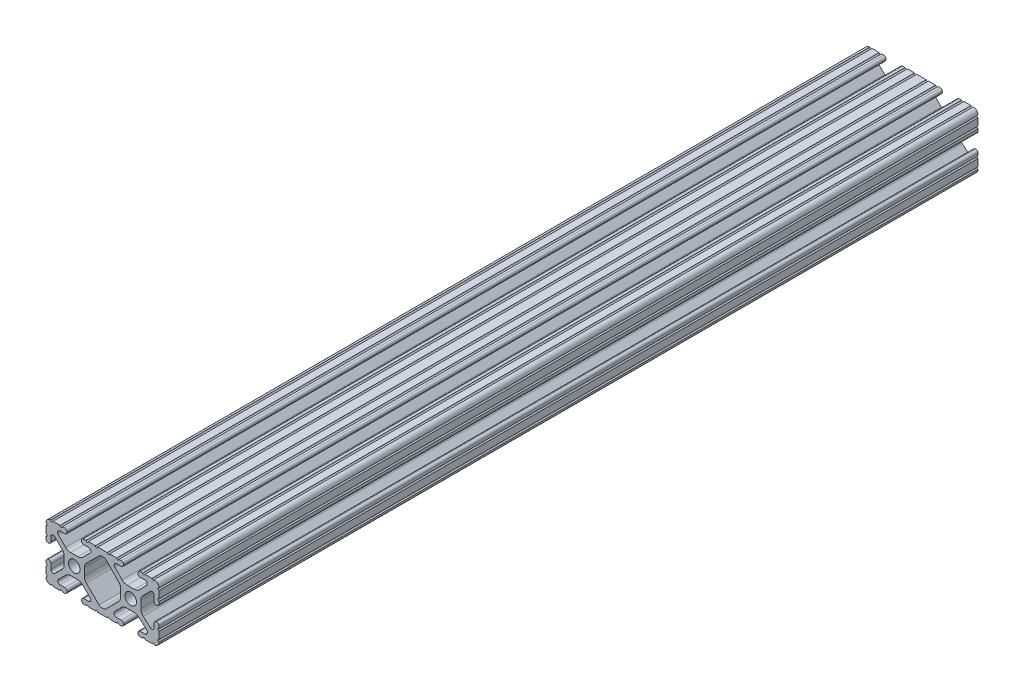
SolidWorks part; units mm, degrees
ref_plane "Front Plane" through (0, 0, 0) normal (0, 0, 1) x (1, 0, 0)
ref_plane "Top Plane" through (0, 0, 0) normal (0, 1, 0) x (1, 0, 0)
ref_plane "Right Plane" through (0, 0, 0) normal (1, 0, 0) x (0, 0, -1)
sketch "Sketch1" plane through (0, 0, 0) normal (0, 0, 1) x (1, 0, 0)
  line L0 (-7.2595, -3.8694) -> (-1.5457, -9.5728)
  line L1 (-8.1915, 1.6223) -> (-8.1915, -1.6223)
  line L2 (-1.504, 9.5765) -> (-7.252, 3.8768)
  line L3 (0.5515, 10.033) -> (-0.3952, 10.033)
  line L4 (7.2829, 3.8459) -> (1.6756, 9.5611)
  line L5 (8.1915, -1.6223) -> (8.1915, 1.6223)
  line L6 (1.5457, -9.5728) -> (7.2595, -3.8694)
  line L7 (-0.4332, -10.033) -> (0.4332, -10.033)
  line L8 (18.0171, 12.7) -> (16.9875, 12.7)
  line L9 (15.9385, 11.651) -> (15.9385, 11.5392)
  line L10 (16.9875, 10.4902) -> (19.1164, 10.4902)
  line L11 (19.8441, 8.7652) -> (16.619, 5.4551)
  line L12 (14.3449, 4.4958) -> (11.0833, 4.4958)
  line L13 (8.817, 5.4472) -> (5.5642, 8.7627)
  line L14 (6.2894, 10.4902) -> (8.4125, 10.4902)
  line L15 (9.4615, 11.5392) -> (9.4615, 11.651)
  line L16 (8.4125, 12.7) -> (7.3829, 12.7)
  line L17 (6.3669, 12.7) -> (3.1496, 12.7)
  line L18 (2.1336, 12.7) -> (-2.1336, 12.7)
  line L19 (-3.1496, 12.7) -> (-6.3669, 12.7)
  line L20 (-7.3829, 12.7) -> (-8.4125, 12.7)
  line L21 (-9.4615, 11.651) -> (-9.4615, 11.5392)
  line L22 (-8.4125, 10.4902) -> (-6.2836, 10.4902)
  line L23 (-5.5326, 8.6661) -> (-8.81, 5.4163)
  line L24 (-11.0455, 4.4958) -> (-14.3545, 4.4958)
  line L25 (-16.59, 5.4163) -> (-19.8674, 8.6661)
  line L26 (-19.1164, 10.4902) -> (-16.9875, 10.4902)
  line L27 (-15.9385, 11.5392) -> (-15.9385, 11.651)
  line L28 (-16.9875, 12.7) -> (-18.0171, 12.7)
  line L29 (-19.0331, 12.7) -> (-22.2504, 12.7)
  line L30 (-25.4, 9.5504) -> (-25.4, 6.3331)
  line L31 (-25.4, 5.3171) -> (-25.4, 4.2375)
  line L32 (-24.401, 3.2385) -> (-24.2392, 3.2385)
  line L33 (-23.1902, 4.2875) -> (-23.1902, 6.3347)
  line L34 (-21.434, 7.0665) -> (-18.148, 3.8082)
  line L35 (-17.2085, 1.5536) -> (-17.2085, -1.6952)
  line L36 (-18.1405, -3.9423) -> (-21.4316, -7.2274)
  line L37 (-23.1902, -6.498) -> (-23.1902, -4.2875)
  line L38 (-24.2392, -3.2385) -> (-24.351, -3.2385)
  line L39 (-25.4, -4.2875) -> (-25.4, -5.3171)
  line L40 (-25.4, -6.3331) -> (-25.4, -9.5504)
  line L41 (-22.2504, -12.7) -> (-19.0331, -12.7)
  line L42 (-18.0171, -12.7) -> (-16.9875, -12.7)
  line L43 (-15.9384, -11.651) -> (-15.9384, -11.5392)
  line L44 (-16.9875, -10.4902) -> (-19.1164, -10.4902)
  line L45 (-19.8341, -8.7551) -> (-16.4966, -5.4237)
  line L46 (-14.2536, -4.4958) -> (-11.1464, -4.4958)
  line L47 (-8.9034, -5.4237) -> (-5.5659, -8.7551)
  line L48 (-6.2836, -10.4902) -> (-8.4125, -10.4902)
  line L49 (-9.4616, -11.5392) -> (-9.4616, -11.651)
  line L50 (-8.4125, -12.7) -> (-7.3829, -12.7)
  line L51 (-6.3669, -12.7) -> (-3.1496, -12.7)
  line L52 (-2.1336, -12.7) -> (2.1336, -12.7)
  line L53 (3.1496, -12.7) -> (6.3669, -12.7)
  line L54 (7.3829, -12.7) -> (8.4125, -12.7)
  line L55 (9.4616, -11.651) -> (9.4616, -11.5392)
  line L56 (8.4125, -10.4902) -> (6.2894, -10.4902)
  line L57 (5.4807, -8.5353) -> (8.5979, -5.4237)
  line L58 (10.8409, -4.4958) -> (14.1026, -4.4958)
  line L59 (16.1879, -5.2766) -> (19.8682, -8.4822)
  line L60 (19.1164, -10.4902) -> (16.9875, -10.4902)
  line L61 (15.9384, -11.5392) -> (15.9384, -11.651)
  line L62 (16.9875, -12.7) -> (18.0171, -12.7)
  line L63 (19.0331, -12.7) -> (22.2504, -12.7)
  line L64 (25.4, -9.5504) -> (25.4, -6.3331)
  line L65 (25.4, -5.3171) -> (25.4, -4.2375)
  line L66 (24.401, -3.2385) -> (24.1892, -3.2385)
  line L67 (23.1902, -4.2375) -> (23.1902, -6.1559)
  line L68 (21.584, -6.8869) -> (18.2982, -4.025)
  line L69 (17.2085, -1.6308) -> (17.2085, 1.6308)
  line L70 (18.1094, 3.8465) -> (21.5263, 7.3534)
  line L71 (23.1902, 6.6769) -> (23.1902, 4.2375)
  line L72 (24.1892, 3.2385) -> (24.401, 3.2385)
  line L73 (25.4, 4.2375) -> (25.4, 5.3171)
  line L74 (25.4, 6.3332) -> (25.4, 9.5504)
  line L75 (22.2504, 12.7) -> (19.0331, 12.7)
  circle A0 centre (-12.7, 0) radius 2.6035
  circle A1 centre (12.7, 0) radius 2.6035
  arc A2 (-1.5457, -9.5728) -> (-0.4332, -10.033) centre (-0.4332, -8.4582) ccw
  arc A3 (-8.1915, -1.6223) -> (-7.2595, -3.8694) centre (-5.0165, -1.6223) ccw
  arc A4 (-7.252, 3.8768) -> (-8.1915, 1.6223) centre (-5.0165, 1.6223) ccw
  arc A5 (-0.3952, 10.033) -> (-1.504, 9.5765) centre (-0.3952, 8.4582) ccw
  arc A6 (1.6756, 9.5611) -> (0.5515, 10.033) centre (0.5515, 8.4582) ccw
  arc A7 (8.1915, 1.6223) -> (7.2829, 3.8459) centre (5.0165, 1.6223) ccw
  arc A8 (7.2595, -3.8694) -> (8.1915, -1.6223) centre (5.0165, -1.6223) ccw
  arc A9 (0.4332, -10.033) -> (1.5457, -9.5728) centre (0.4332, -8.4582) ccw
  arc A10 (18.0171, 12.7) -> (19.0331, 12.7) centre (18.5251, 12.7) ccw
  arc A11 (16.9875, 12.7) -> (15.9385, 11.651) centre (16.9875, 11.651) ccw
  arc A12 (15.9385, 11.5392) -> (16.9875, 10.4902) centre (16.9875, 11.5392) ccw
  arc A13 (19.8441, 8.7652) -> (19.1164, 10.4902) centre (19.1164, 9.4742) ccw
  arc A14 (14.3449, 4.4958) -> (16.619, 5.4551) centre (14.3449, 7.6708) ccw
  arc A15 (8.817, 5.4472) -> (11.0833, 4.4958) centre (11.0833, 7.6708) ccw
  arc A16 (6.2894, 10.4902) -> (5.5642, 8.7627) centre (6.2894, 9.4742) ccw
  arc A17 (8.4125, 10.4902) -> (9.4615, 11.5392) centre (8.4125, 11.5392) ccw
  arc A18 (9.4615, 11.651) -> (8.4125, 12.7) centre (8.4125, 11.651) ccw
  arc A19 (6.3669, 12.7) -> (7.3829, 12.7) centre (6.8749, 12.7) ccw
  arc A20 (2.1336, 12.7) -> (3.1496, 12.7) centre (2.6416, 12.7) ccw
  arc A21 (-3.1496, 12.7) -> (-2.1336, 12.7) centre (-2.6416, 12.7) ccw
  arc A22 (-7.3829, 12.7) -> (-6.3669, 12.7) centre (-6.8749, 12.7) ccw
  arc A23 (-8.4125, 12.7) -> (-9.4615, 11.651) centre (-8.4125, 11.651) ccw
  arc A24 (-9.4615, 11.5392) -> (-8.4125, 10.4902) centre (-8.4125, 11.5392) ccw
  arc A25 (-5.5326, 8.6661) -> (-6.2836, 10.4902) centre (-6.2836, 9.4235) ccw
  arc A26 (-11.0455, 4.4958) -> (-8.81, 5.4163) centre (-11.0455, 7.6708) ccw
  arc A27 (-16.59, 5.4163) -> (-14.3545, 4.4958) centre (-14.3545, 7.6708) ccw
  arc A28 (-19.1164, 10.4902) -> (-19.8674, 8.6661) centre (-19.1164, 9.4235) ccw
  arc A29 (-16.9875, 10.4902) -> (-15.9385, 11.5392) centre (-16.9875, 11.5392) ccw
  arc A30 (-15.9385, 11.651) -> (-16.9875, 12.7) centre (-16.9875, 11.651) ccw
  arc A31 (-19.0331, 12.7) -> (-18.0171, 12.7) centre (-18.5251, 12.7) ccw
  arc A32 (-23.2664, 12.6998) -> (-22.2504, 12.7) centre (-22.7584, 12.7) ccw
  arc A33 (-23.2664, 12.6998) -> (-25.3998, 10.5664) centre (-23.2918, 10.5918) ccw
  arc A34 (-25.4, 9.5504) -> (-25.3998, 10.5664) centre (-25.4, 10.0584) ccw
  arc A35 (-25.4, 5.3171) -> (-25.4, 6.3331) centre (-25.4, 5.8251) ccw
  arc A36 (-25.4, 4.2375) -> (-24.401, 3.2385) centre (-24.401, 4.2375) ccw
  arc A37 (-24.2392, 3.2385) -> (-23.1902, 4.2875) centre (-24.2392, 4.2875) ccw
  arc A38 (-21.434, 7.0665) -> (-23.1902, 6.3347) centre (-22.1596, 6.3347) ccw
  arc A39 (-17.2085, 1.5536) -> (-18.148, 3.8082) centre (-20.3835, 1.5536) ccw
  arc A40 (-18.1405, -3.9423) -> (-17.2085, -1.6952) centre (-20.3835, -1.6952) ccw
  arc A41 (-23.1902, -6.498) -> (-21.4316, -7.2274) centre (-22.1596, -6.498) ccw
  arc A42 (-23.1902, -4.2875) -> (-24.2392, -3.2385) centre (-24.2392, -4.2875) ccw
  arc A43 (-24.351, -3.2385) -> (-25.4, -4.2875) centre (-24.351, -4.2875) ccw
  arc A44 (-25.4, -6.3331) -> (-25.4, -5.3171) centre (-25.4, -5.8251) ccw
  arc A45 (-25.3998, -10.5664) -> (-25.4, -9.5504) centre (-25.4, -10.0584) ccw
  arc A46 (-25.3998, -10.5664) -> (-23.2664, -12.6998) centre (-23.2918, -10.5918) ccw
  arc A47 (-22.2504, -12.7) -> (-23.2664, -12.6998) centre (-22.7584, -12.7) ccw
  arc A48 (-18.0171, -12.7) -> (-19.0331, -12.7) centre (-18.5251, -12.7) ccw
  arc A49 (-16.9875, -12.7) -> (-15.9384, -11.651) centre (-16.9875, -11.651) ccw
  arc A50 (-15.9384, -11.5392) -> (-16.9875, -10.4902) centre (-16.9875, -11.5392) ccw
  arc A51 (-19.8341, -8.7551) -> (-19.1164, -10.4902) centre (-19.1164, -9.4742) ccw
  arc A52 (-14.2536, -4.4958) -> (-16.4966, -5.4237) centre (-14.2536, -7.6708) ccw
  arc A53 (-8.9034, -5.4237) -> (-11.1464, -4.4958) centre (-11.1464, -7.6708) ccw
  arc A54 (-6.2836, -10.4902) -> (-5.5659, -8.7551) centre (-6.2836, -9.4742) ccw
  arc A55 (-8.4125, -10.4902) -> (-9.4616, -11.5392) centre (-8.4125, -11.5392) ccw
  arc A56 (-9.4616, -11.651) -> (-8.4125, -12.7) centre (-8.4125, -11.651) ccw
  arc A57 (-6.3669, -12.7) -> (-7.3829, -12.7) centre (-6.8749, -12.7) ccw
  arc A58 (-2.1336, -12.7) -> (-3.1496, -12.7) centre (-2.6416, -12.7) ccw
  arc A59 (3.1496, -12.7) -> (2.1336, -12.7) centre (2.6416, -12.7) ccw
  arc A60 (7.3829, -12.7) -> (6.3669, -12.7) centre (6.8749, -12.7) ccw
  arc A61 (8.4125, -12.7) -> (9.4616, -11.651) centre (8.4125, -11.651) ccw
  arc A62 (9.4616, -11.5392) -> (8.4125, -10.4902) centre (8.4125, -11.5392) ccw
  arc A63 (5.4807, -8.5353) -> (6.2894, -10.4902) centre (6.2894, -9.3455) ccw
  arc A64 (10.8409, -4.4958) -> (8.5979, -5.4237) centre (10.8409, -7.6708) ccw
  arc A65 (16.1879, -5.2766) -> (14.1026, -4.4958) centre (14.1026, -7.6708) ccw
  arc A66 (19.1164, -10.4902) -> (19.8682, -8.4822) centre (19.1164, -9.3455) ccw
  arc A67 (16.9875, -10.4902) -> (15.9384, -11.5392) centre (16.9875, -11.5392) ccw
  arc A68 (15.9384, -11.651) -> (16.9875, -12.7) centre (16.9875, -11.651) ccw
  arc A69 (19.0331, -12.7) -> (18.0171, -12.7) centre (18.5251, -12.7) ccw
  arc A70 (23.2664, -12.6998) -> (22.2504, -12.7) centre (22.7584, -12.7) ccw
  arc A71 (23.2664, -12.6998) -> (25.3998, -10.5664) centre (23.2918, -10.5918) ccw
  arc A72 (25.4, -9.5504) -> (25.3998, -10.5664) centre (25.4, -10.0584) ccw
  arc A73 (25.4, -5.3171) -> (25.4, -6.3331) centre (25.4, -5.8251) ccw
  arc A74 (25.4, -4.2375) -> (24.401, -3.2385) centre (24.401, -4.2375) ccw
  arc A75 (24.1892, -3.2385) -> (23.1902, -4.2375) centre (24.1892, -4.2375) ccw
  arc A76 (21.584, -6.8869) -> (23.1902, -6.1559) centre (22.2207, -6.1559) ccw
  arc A77 (17.2085, -1.6308) -> (18.2982, -4.025) centre (20.3835, -1.6308) ccw
  arc A78 (18.1094, 3.8465) -> (17.2085, 1.6308) centre (20.3835, 1.6308) ccw
  arc A79 (23.1902, 6.6769) -> (21.5263, 7.3534) centre (22.2207, 6.6769) ccw
  arc A80 (23.1902, 4.2375) -> (24.1892, 3.2385) centre (24.1892, 4.2375) ccw
  arc A81 (24.401, 3.2385) -> (25.4, 4.2375) centre (24.401, 4.2375) ccw
  arc A82 (25.4, 6.3332) -> (25.4, 5.3171) centre (25.4, 5.8251) ccw
  arc A83 (25.3998, 10.5664) -> (25.4, 9.5504) centre (25.4, 10.0584) ccw
  arc A84 (25.3998, 10.5664) -> (23.2664, 12.6998) centre (23.2918, 10.5918) ccw
  arc A85 (22.2504, 12.7) -> (23.2664, 12.6998) centre (22.7584, 12.7) ccw
  point P248 (0, 10.033)
extrude "Boss-Extrude1" add sketch "Sketch1" along normal mid plane 368.3
